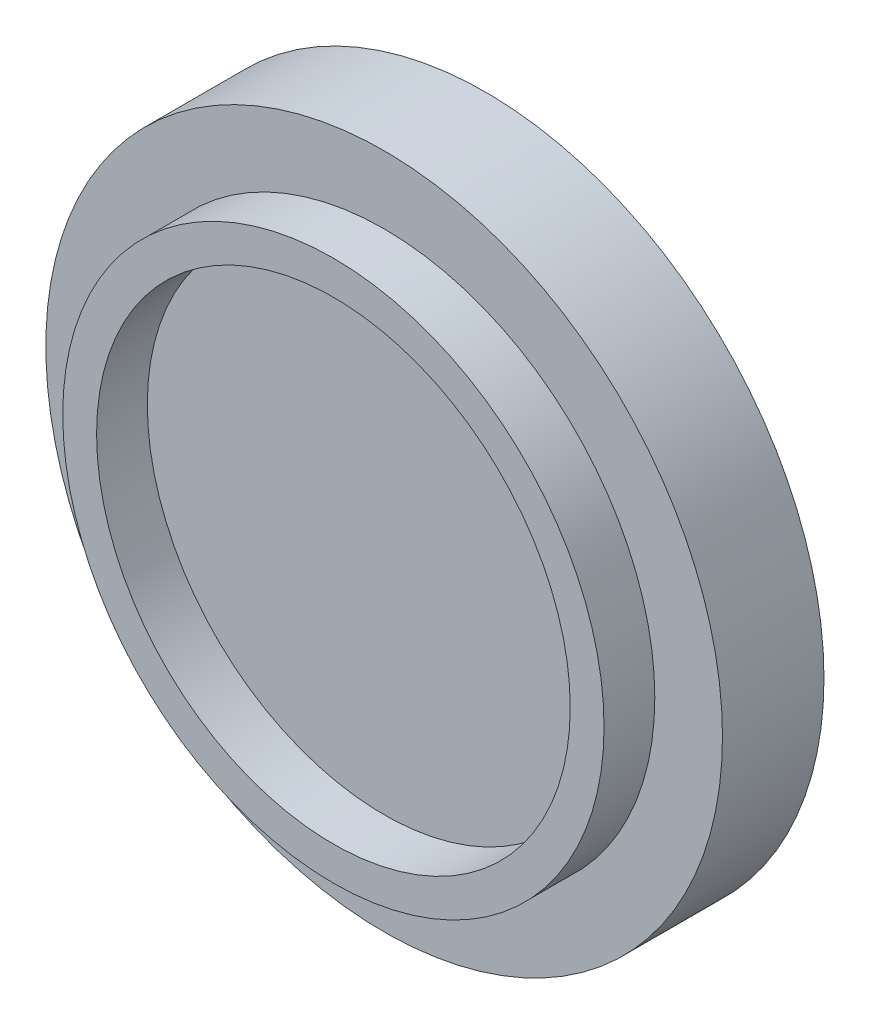
SolidWorks part; units mm, degrees
ref_plane "Płaszczyzna przednia" through (0, 0, 0) normal (0, 0, 1) x (1, 0, 0)
ref_plane "Płaszczyzna górna" through (0, 0, 0) normal (0, 1, 0) x (1, 0, 0)
ref_plane "Płaszczyzna prawa" through (0, 0, 0) normal (1, 0, 0) x (0, 0, -1)
sketch "Szkic1" plane through (0, 0, 0) normal (0, 0, 1) x (1, 0, 0)
  circle A0 centre (0, 0) radius 100
extrude "Dodanie-wyciągnięcie1" add sketch "Szkic1" along normal blind 30
sketch "Szkic2" plane through (0, 0, 30) normal (0, 0, 1) x (1, 0, 0)
  circle A0 centre (0, 0) radius 80
  circle A1 centre (0, 0) radius 70
extrude "Dodanie-wyciągnięcie2" add sketch "Szkic2" along normal blind 15
